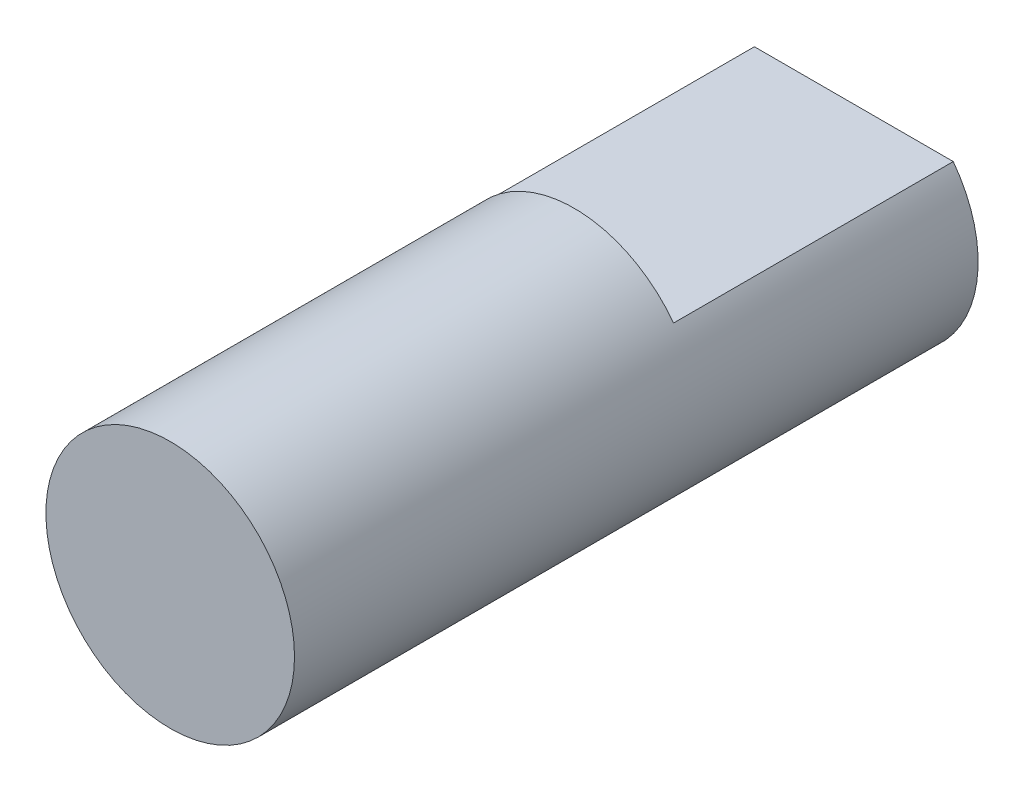
SolidWorks part; units mm, degrees
ref_plane "Alzado" through (0, 0, 0) normal (0, 0, 1) x (1, 0, 0)
ref_plane "Planta" through (0, 0, 0) normal (0, 1, 0) x (1, 0, 0)
ref_plane "Vista lateral" through (0, 0, 0) normal (1, 0, 0) x (0, 0, -1)
sketch "Croquis1" plane through (0, 0, 0) normal (0, 0, 1) x (1, 0, 0)
  circle A0 centre (0, 0) radius 4
extrude "Saliente-Extruir1" add sketch "Croquis1" along normal mid plane 22 contours A0
sketch "Croquis2" plane through (0, 0, -11) normal (0, 0, -1) x (-1, 0, 0)
  line L0 (0, -4) -> (0, 2.4) construction
  line L1 (0, 2.4) -> (-3.2, 2.4) construction
  line L2 (0.0405, 2.4) -> (3.2, 2.4) construction
  line L3 (-3.2, 2.4) -> (3.2, 2.4)
  circle A0 centre (0, 0) radius 4 construction
  arc A1 (-3.2, 2.4) -> (3.2, 2.4) centre (0, 0) cw
extrude "Cortar-Extruir1" cut sketch "Croquis2" against normal blind 9 contours L3 A1
